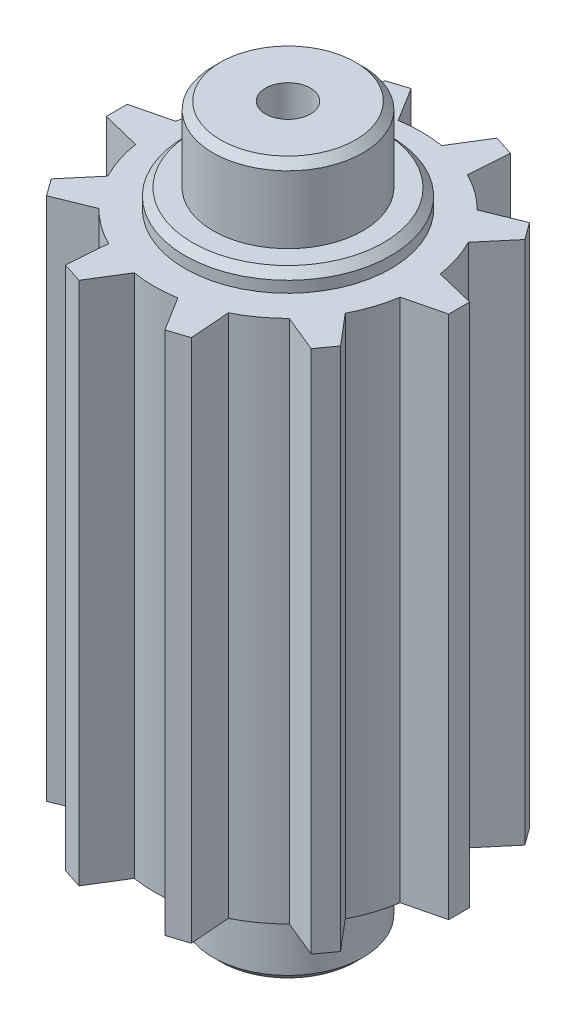
SolidWorks part; units mm, degrees
ref_plane "Front Plane" through (0, 0, 0) normal (0, 0, 1) x (1, 0, 0)
ref_plane "Top Plane" through (0, 0, 0) normal (0, 1, 0) x (1, 0, 0)
ref_plane "Right Plane" through (0, 0, 0) normal (1, 0, 0) x (0, 0, -1)
sketch "Sketch1" plane through (0, 0, 0) normal (0, 1, 0) x (1, 0, 0)
  line L3 (4.57, 0) -> (4.57, -0.28)
  line L4 (4.57, 0) -> (4.57, 0.28)
  line L5 (4.57, -0.28) -> (3.2654, -0.5999)
  line L6 (4.57, 0.28) -> (3.2654, 0.5999)
  circle A0 centre (0, 0) radius 3.57
  arc A3 (3.2654, -0.5999) -> (3.2654, 0.5999) centre (0, 0) ccw
  point P3 (3.32, 0)
  point P10 (4.57, 0)
  dimension "D1" = 7.14
  dimension "D2" = 3.32
  dimension "D5" = 4.57
  dimension "D6" = 0.28
  dimension "D7" = 0.28
  dimension "D8" = 1.3433
  dimension "D9" = 1.3433
extrude "Boss-Extrude3" add sketch "Sketch1" along normal blind 14 contours L5 A3 L6 A0 | A3 L5 A0 L6 | A0 L5 L3 L4 L6
pattern_circular "CirPattern2" count 10 over 360 about axis through (0, 0, 0) along (0, 1, 0) of "Boss-Extrude3"
sketch "Sketch3" plane through (0, 14, 0) normal (0, 1, 0) x (1, 0, 0)
  circle A0 centre (0, 0) radius 2.75
  dimension "D1" = 5.5
extrude "Boss-Extrude4" add sketch "Sketch3" along normal blind 0.5
sketch "Sketch4" plane through (0, 0, 0) normal (0, -1, 0) x (1, 0, 0)
  circle A0 centre (0, 0) radius 2.75
  dimension "D1" = 5.5
extrude "Boss-Extrude5" add sketch "Sketch4" along normal blind 0.5
sketch "Sketch5" plane through (0, 14.5, 0) normal (0, 1, 0) x (1, 0, 0)
  circle A0 centre (0, 0) radius 2
  dimension "D1" = 4
extrude "Boss-Extrude6" add sketch "Sketch5" along normal blind 2
sketch "Sketch6" plane through (0, -0.5, 0) normal (0, -1, 0) x (1, 0, 0)
  circle A1 centre (0, 0) radius 2
  dimension "D1" = 4
extrude "Boss-Extrude7" add sketch "Sketch6" along normal blind 2
chamfer "Chamfer1" distance 0.2 angle 45 4 edges at (0, -0.5, -2.75) (0, -2.5, -2) (0, 14.5, 2.75) (0, 16.5, 2)
sketch "Sketch7" plane through (0, -2.5, 0) normal (0, -1, 0) x (1, 0, 0)
  circle A0 centre (0, 0) radius 0.6
  dimension "D1" = 1.2
extrude "Cut-Extrude1" cut sketch "Sketch7" against normal through all
